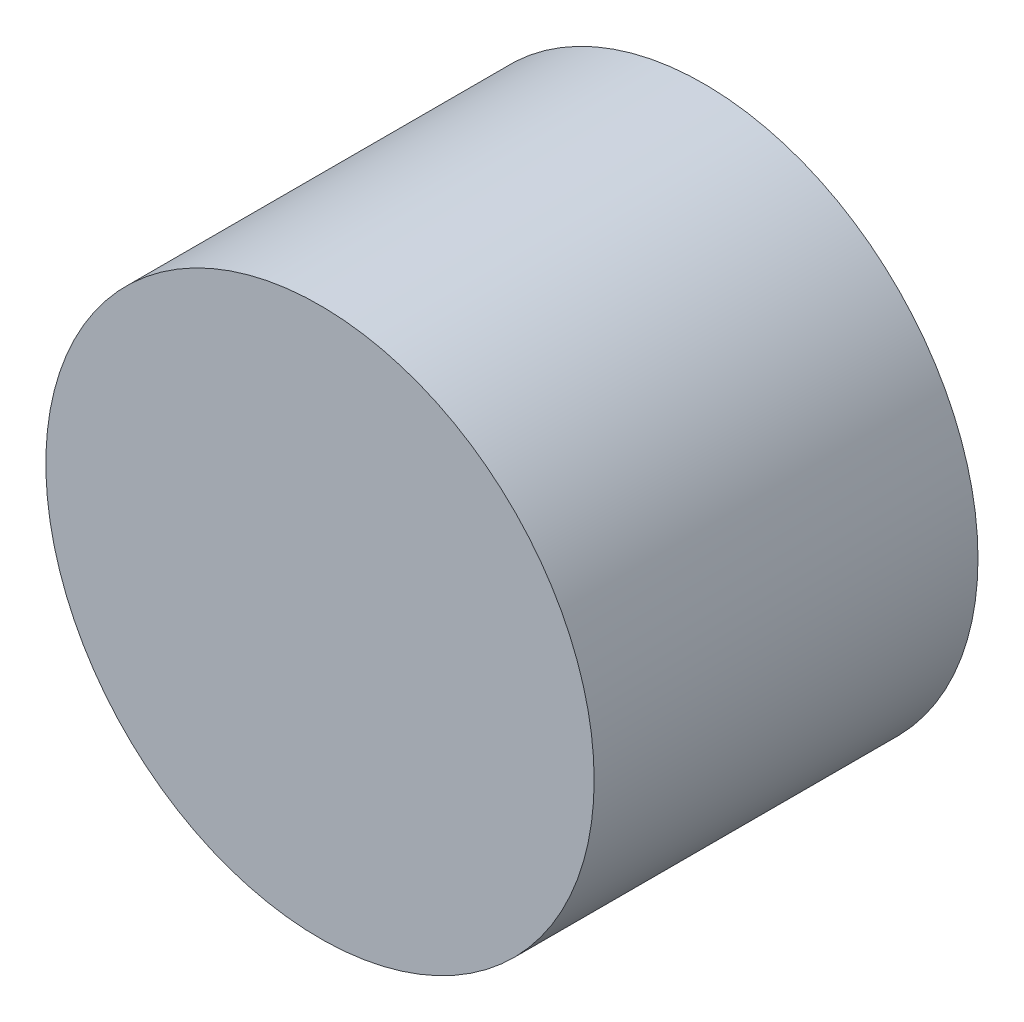
SolidWorks part; units mm, degrees
ref_plane "Front Plane" through (0, 0, 0) normal (0, 0, 1) x (1, 0, 0)
ref_plane "Top Plane" through (0, 0, 0) normal (0, 1, 0) x (1, 0, 0)
ref_plane "Right Plane" through (0, 0, 0) normal (1, 0, 0) x (0, 0, -1)
sketch "Sketch1" plane through (0, 0, 0) normal (0, 0, 1) x (1, 0, 0)
  circle A0 centre (0, 0) radius 63.5
  dimension "D1" = 127
extrude "Boss-Extrude1" add sketch "Sketch1" along normal mid plane 88.9
